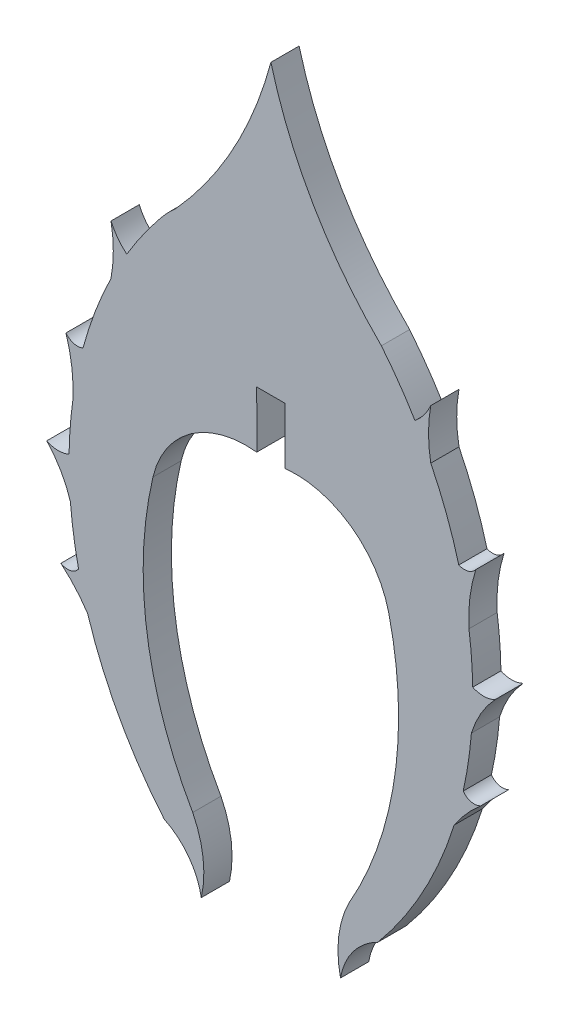
SolidWorks part; units mm, degrees
ref_plane "Front Plane" through (0, 0, 0) normal (0, 0, 1) x (1, 0, 0)
ref_plane "Top Plane" through (0, 0, 0) normal (0, 1, 0) x (1, 0, 0)
ref_plane "Right Plane" through (0, 0, 0) normal (1, 0, 0) x (0, 0, -1)
sketch "Sketch1" plane through (0, 0, 0) normal (0, 0, 1) x (1, 0, 0)
  line L0 (-0.7601, 7.461) -> (0.7679, 7.46)
  line L1 (0.7679, 7.46) -> (0.7659, 4.411)
  line L2 (-0.7591, 4.4111) -> (-0.7601, 7.461)
  arc A0 (6.3724, 0.4469) -> (0.7659, 4.411) centre (1.3363, -0.7289) ccw
  arc A1 (4.2265, -14.172) -> (6.3724, 0.4469) centre (-13.2366, -4.1417) ccw
  arc A2 (10.3912, -5.8643) -> (10.8334, -2.9332) centre (-11.0724, -1.1273) ccw
  arc A3 (5.7708, -15.2493) -> (9.9019, -7.7001) centre (-11.0724, -1.1273) ccw
  arc A5 (-7.7794, 10.1615) -> (-5.9633, 12.7522) centre (11.0802, -1.1273) cw
  arc A6 (-10.1439, 4.5877) -> (-8.6316, 8.5972) centre (11.0802, -1.1273) cw
  arc A7 (-10.8966, -0.7497) -> (-10.6931, 1.8806) centre (11.0802, -1.1273) cw
  arc A8 (-3.7554, -17.9226) -> (-5.763, -15.2493) centre (-7.3795, -18.5538) ccw
  arc A9 (5.9711, 12.7522) -> (0.0048, 23.0286) centre (21.9265, 28.8859) cw
  arc A10 (8.6394, 8.5972) -> (8.6394, 11.29) centre (15.9233, 9.9436) cw
  arc A11 (8.6394, 11.29) -> (7.7872, 10.1615) centre (5.802, 12.5466) cw
  arc A12 (10.7009, 1.8806) -> (11.0722, 4.8356) centre (18.8382, 2.3588) cw
  arc A13 (11.0722, 4.8356) -> (10.1517, 4.5877) centre (10.4519, 5.306) cw
  arc A14 (10.8334, -2.9332) -> (12.1093, -0.7289) centre (16.2439, -4.5937) cw
  arc A15 (12.1093, -0.7289) -> (10.9044, -0.7497) centre (11.4856, 0.4998) cw
  arc A16 (9.9019, -7.7001) -> (11.3457, -6.0749) centre (16.2964, -11.9269) cw
  arc A17 (11.3457, -6.0749) -> (10.3912, -5.8643) centre (10.9811, -5.4591) cw
  arc A18 (4.2265, -14.172) -> (3.7632, -17.9226) centre (9.193, -16.6894) ccw
  arc A19 (3.7632, -17.9226) -> (5.7708, -15.2493) centre (7.3873, -18.5538) cw
  arc A20 (10.9044, -0.7497) -> (10.7009, 1.8806) centre (-11.0724, -1.1273) ccw
  arc A21 (10.1517, 4.5877) -> (8.6394, 8.5972) centre (-11.0724, -1.1273) ccw
  arc A22 (7.7872, 10.1615) -> (5.9711, 12.7522) centre (-11.0724, -1.1273) ccw
  arc A23 (-4.2187, -14.172) -> (-3.7554, -17.9226) centre (-9.1851, -16.6894) cw
  arc A24 (-11.3379, -6.0749) -> (-10.3834, -5.8643) centre (-10.9733, -5.4591) ccw
  arc A25 (-9.8941, -7.7001) -> (-11.3379, -6.0749) centre (-16.2885, -11.9269) ccw
  arc A26 (-12.1015, -0.7289) -> (-10.8966, -0.7497) centre (-11.4777, 0.4998) ccw
  arc A27 (-10.8255, -2.9332) -> (-12.1015, -0.7289) centre (-16.2361, -4.5937) ccw
  arc A28 (-11.0644, 4.8356) -> (-10.1439, 4.5877) centre (-10.4441, 5.306) ccw
  arc A29 (-10.6931, 1.8806) -> (-11.0644, 4.8356) centre (-18.8304, 2.3588) ccw
  arc A30 (-8.6316, 11.29) -> (-7.7794, 10.1615) centre (-5.7942, 12.5466) ccw
  arc A31 (-8.6316, 8.5972) -> (-8.6316, 11.29) centre (-15.9155, 9.9436) ccw
  arc A32 (-5.1104, 13.6428) -> (0.0048, 23.0286) centre (-21.9162, 28.8886) ccw
  arc A33 (-5.9633, 12.7522) -> (-5.1104, 13.6428) centre (0.003, 7.8921) cw
  arc A34 (-5.763, -15.2493) -> (-9.8941, -7.7001) centre (11.0802, -1.1273) cw
  arc A35 (-10.3834, -5.8643) -> (-10.8255, -2.9332) centre (11.0802, -1.1273) cw
  arc A36 (-4.2187, -14.172) -> (-6.3645, 0.4469) centre (13.2444, -4.1417) cw
  arc A37 (-6.3645, 0.4469) -> (-0.7591, 4.4111) centre (-1.3285, -0.7289) cw
extrude "Boss-Extrude1" add sketch "Sketch1" along normal blind 1.524
